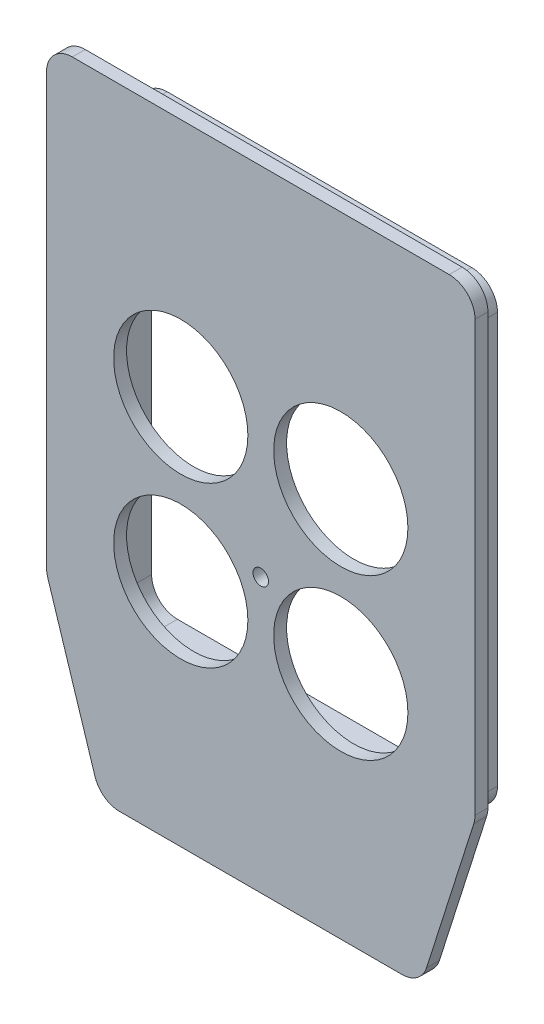
SolidWorks part; units mm, degrees
material "PEI"
ref_plane "Front Plane" through (0, 0, 0) normal (0, 0, 1) x (1, 0, 0)
ref_plane "Top Plane" through (0, 0, 0) normal (0, 1, 0) x (1, 0, 0)
ref_plane "Right Plane" through (0, 0, 0) normal (1, 0, 0) x (0, 0, -1)
sketch "Sketch1" plane through (0, 0, 0) normal (0, 0, 1) x (1, 0, 0)
  line L0 (0, 0) -> (10.5, -33)
  line L2 (0, 0) -> (0, 89)
  line L3 (0, 89) -> (83, 89)
  line L4 (83, 0) -> (83, 89)
  line L5 (10.5, -33) -> (72.5, -33)
  line L6 (72.5, -33) -> (83, 0)
  circle A0 centre (26, 42.5) radius 13
  circle A1 centre (57, 42.5) radius 13
  circle A2 centre (26, 11.5) radius 13
  circle A3 centre (57, 11.5) radius 13
  circle A4 centre (41.5, 19.99) radius 1.5
  point P5 (41.5, -33)
  point P8 (41.5, 89)
  point P19 (0, 0)
  dimension "D5" = 26
  dimension "D10" = 3
  dimension "D1" = 83
  dimension "D2" = 89
  dimension "D3" = 62
  dimension "D4" = 122
  dimension "D6" = 46.5
  dimension "D7" = 31
  dimension "D8" = 31
  dimension "D9" = 15.5
  dimension "D11" = 69.01
extrude "Boss-Extrude1" add sketch "Sketch1" along normal blind 2.5
sketch "Sketch2" plane through (0, 0, 0) normal (0, 0, -1) x (-1, 0, 0)
  line L0 (-74, 79) -> (-74, -6.5)
  line L1 (-76, 81) -> (-7, 81)
  line L2 (-76, 81) -> (-76, -8.5)
  line L3 (-76, -8.5) -> (-7, -8.5)
  line L4 (-7, 81) -> (-7, -8.5)
  line L5 (-74, -6.5) -> (-9, -6.5)
  line L6 (0, 0) -> (0, 89)
  line L7 (0, 89) -> (-83, 89)
  line L8 (-83, 89) -> (-83, 0)
  line L9 (-83, 0) -> (-72.5, -33)
  line L10 (-72.5, -33) -> (-10.5, -33)
  line L11 (-10.5, -33) -> (0, 0)
  line L12 (0, 0) -> (0, 89)
  line L13 (0, 89) -> (-83, 89)
  line L14 (-83, 89) -> (-83, 0)
  line L15 (-83, 0) -> (-72.5, -33)
  line L16 (-72.5, -33) -> (-10.5, -33)
  line L17 (-10.5, -33) -> (0, 0)
  line L18 (-9, 79) -> (-9, -6.5)
  line L19 (-74, 79) -> (-9, 79)
  circle A0 centre (-26, 11.5) radius 13 construction
  circle A1 centre (-57, 11.5) radius 13 construction
  circle A2 centre (-26, 42.5) radius 13 construction
  circle A3 centre (-57, 42.5) radius 13 construction
  circle A4 centre (-26, 11.5) radius 13
  circle A5 centre (-57, 11.5) radius 13
  circle A6 centre (-26, 42.5) radius 13
  circle A7 centre (-57, 42.5) radius 13
  dimension "D2" = 7
  dimension "D3" = 7
  dimension "D4" = 8
  dimension "D5" = 20
  dimension "D1" = 0
extrude "Boss-Extrude2" add sketch "Sketch2" along normal blind 8.85 contours L4 L1 L2 L3 L0 L19 L18 L5
fillet "Fillet1" radius 5 14 edges at (0, 89, 1.25) (83, 89, 1.25) (83, 0, 1.25) (72.5, -33, 1.25) (10.5, -33, 1.25) (0, 0, 1.25) (7, -8.5, -4.425) (76, -8.5, -4.425) (74, -6.5, -4.425) (9, -6.5, -4.425) (9, 79, -4.425) (7, 81, -4.425) (74, 79, -4.425) (76, 81, -4.425)
ref_plane "Plane1" through (41.5, 0, 0) normal (1, 0, 0) x (0, 0, -1)
